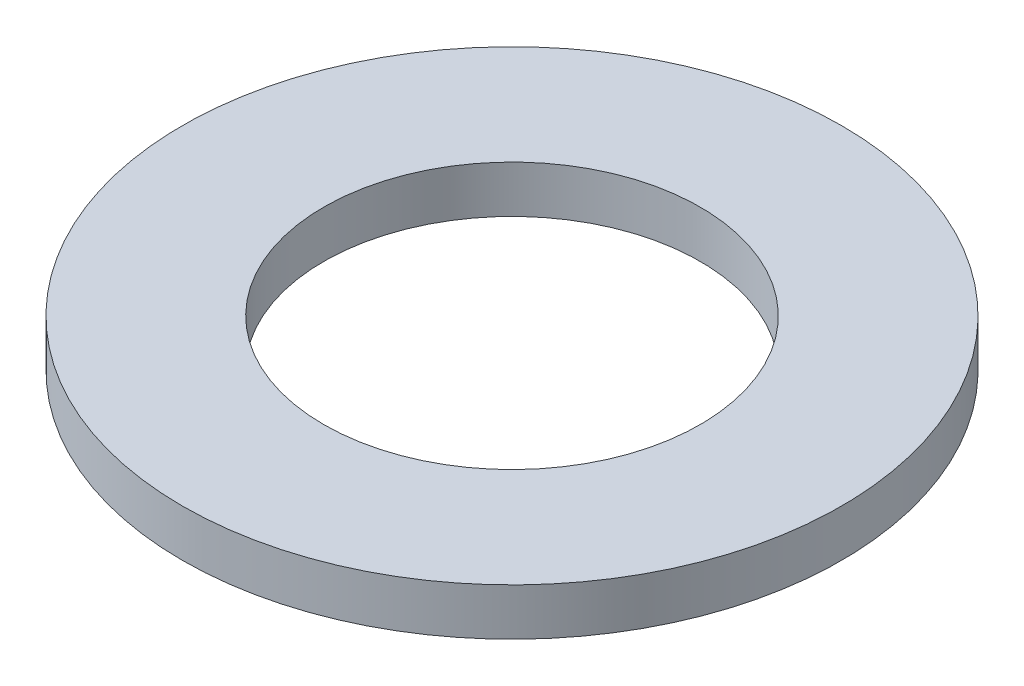
SolidWorks part; units mm, degrees
ref_plane "Front Plane" through (0, 0, 0) normal (0, 0, 1) x (1, 0, 0)
ref_plane "Top Plane" through (0, 0, 0) normal (0, 1, 0) x (1, 0, 0)
ref_plane "Right Plane" through (0, 0, 0) normal (1, 0, 0) x (0, 0, -1)
sketch "Sketch1" plane through (0, 0, 0) normal (0, 1, 0) x (1, 0, 0)
  circle A0 centre (0, 0) radius 12.7
  circle A1 centre (0, 0) radius 22.225
  dimension "D1" = 25.4
  dimension "D2" = 9.525
extrude "Boss-Extrude1" add sketch "Sketch1" along normal blind 3.175
